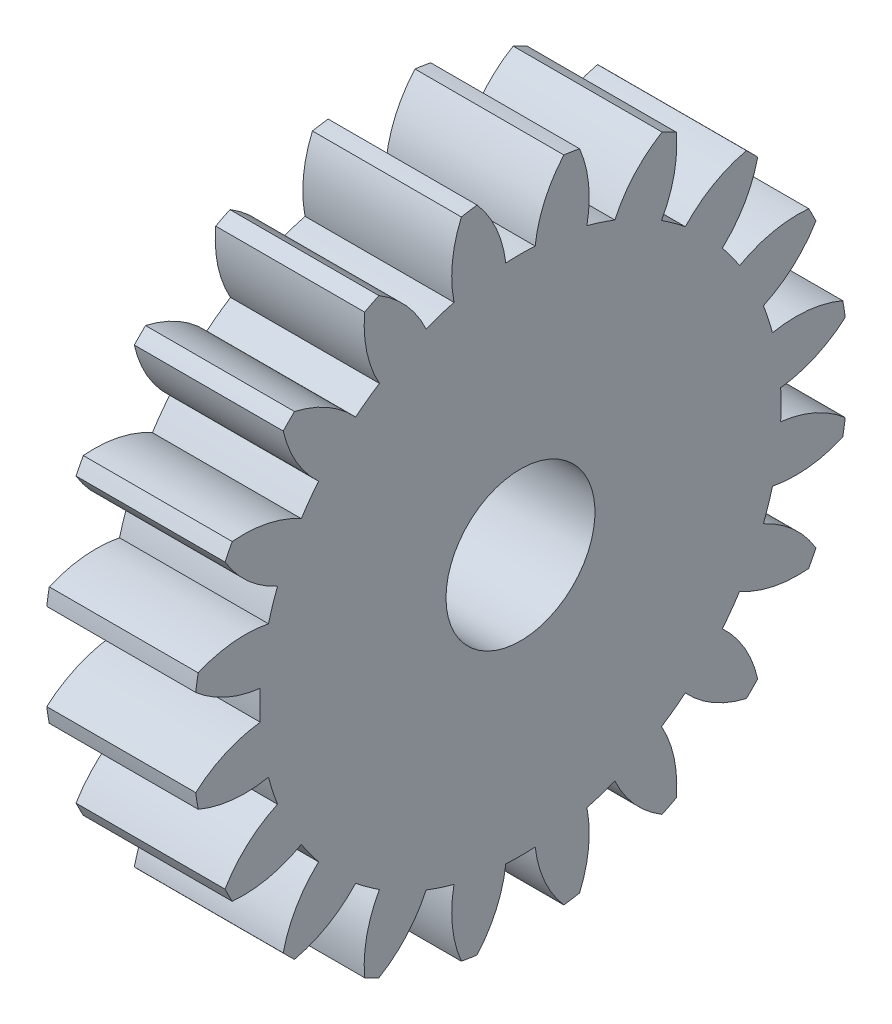
SolidWorks part; units mm, degrees
material "Pine"
ref_plane "Plane1" through (0, 0, 0) normal (0, 0, 1) x (1, 0, 0)
ref_plane "Plane2" through (0, 0, 0) normal (0, 1, 0) x (1, 0, 0)
ref_plane "Plane3" through (0, 0, 0) normal (1, 0, 0) x (0, 0, -1)
sketch "HoldingSke" plane through (0, 0, 0) normal (0, 1, 0) x (1, 0, 0)
  line L0 (0, 0) -> (0.4698, -0.171)
  line L1 (-15, 0) -> (100, 0) construction
  line L2 (0, 0) -> (-2.1039, 2.3779)
  line L3 (0, 0) -> (-11.863, 4.5341)
  line L4 (0, 0) -> (8.1152, 2.9537)
  line L5 (0, 0) -> (-46.8476, -17.4728)
  line L6 (0, 0) -> (-8.2896, -5.593)
  line L7 (-2.1039, 2.3779) -> (8.6586, 51.2059)
  line L8 (-76.2, 54.61) -> (-74.4, 54.61)
  line L9 (-71.009, 38.7566) -> (-53.1078, 45.2721)
  line L10 (-76.2, 71.12) -> (104.1128, 71.12)
  line L11 (0, 0) -> (-10, 0)
  line L12 (-76.2, 101.6) -> (-76.133, 101.6)
  line L13 (24.9733, 27.94) -> (52.9518, 28.4284)
  line L14 (24.9733, 27.94) -> (24.9743, 27.94)
  line L15 (24.9733, 27.94) -> (100.4006, 29.5858)
  line L16 (-63.627, -2) -> (-12.827, -2)
  circle A0 centre (0, 0) radius 5
  circle A1 centre (0, 0) radius 17.499
  circle A2 centre (0, 0) radius 37.5
  circle A3 centre (0, 0) radius 5
  dimension "MHD" = 34.998
  dimension "Hub_dia" = 75
  dimension "Bore" = 10
  dimension "MBD" = 10
  dimension "Num_teeth" = 20
  dimension "Pitch" = 0.5
  dimension "Overall_len" = 50
  dimension "Show_teeth" = 20
  dimension "Thickness" = 10
  dimension "OAL" = 50.0001
  dimension "T_dim" = 1.8
  dimension "Ap" = 20
  dimension "H" = 19.05
  dimension "Pitch_radius" = 180.3128
  dimension "Width" = 10
  dimension "Backlash" = 0.067
  dimension "Addendum_fac" = 1
  dimension "Dedendum_fac" = 1.25
  dimension "Clearance_fac" = 0.25
  dimension "Dedendum_add" = 0.001
  dimension "Module" = 2
sketch "BasProSke" plane through (0, 0, 0) normal (0, 1, 0) x (1, 0, 0)
  line L0 (-10, 0) -> (60, 0) construction
  line L1 (0, 0) -> (0, 22)
  line L2 (0, 0) -> (10, 0)
  line L3 (10, 0) -> (10, 22)
  line L4 (10, 22) -> (0, 22)
  dimension "Thickness" = 10
  dimension "Diameter" = 44
revolve "Base-Revolve" add sketch "BasProSke" angle 360 about L0
sketch "TooCutSke" plane through (0, 0, 0) normal (1, 0, 0) x (0, 0, -1)
  line L1 (0, 0) -> (0, 107) construction
  line L2 (0, 0) -> (-1.6864, 19.9288) construction
  line L3 (0, 0) -> (-6.2409, 39.4033) construction
  line L4 (-1.6864, 19.9288) -> (-3.1204, 19.7016) construction
  arc A0 (0.9862, 17.4712) -> (-0.9862, 17.4712) centre (0, 0) ccw
  arc A1 (2.9329, 21.8293) -> (-2.9329, 21.8293) centre (0, 0) ccw
  circle A2 centre (0, 0) radius 20 construction
  circle A3 centre (0, 0) radius 18.7939 construction
  arc A4 (-0.9862, 17.4712) -> (-2.9329, 21.8293) centre (-8.9313, 16.536) ccw
  arc A5 (2.9329, 21.8293) -> (0.9862, 17.4712) centre (8.9313, 16.536) ccw
  dimension "Root_dia" = 34.998
  dimension "Overcut_dia" = 44.0508
  dimension "Pitch_dia" = 40
  dimension "Base_dia" = 37.5877
  dimension "Flank_rad" = 8
  dimension "Half_ang" = 9
  dimension "Half_CT" = 1.4519
extrude "ToothCut" cut sketch "TooCutSke" along normal through all
fillet "Breaks" [suppressed] radius 0.04
fillet "RootFillets" [suppressed] radius 0.501
pattern_circular "TeethCuts" count 20 every 18 about axis through (-10, 0, 0) along (1, 0, 0) of "ToothCut", "RootFillets", "Breaks"
sketch "HubNeaOneSke" plane through (0, 0, 0) normal (-1, 0, 0) x (0, 0, 1)
  circle A0 centre (0, 0) radius 17.499
  dimension "Diameter" = 34.998
extrude "HubNearOne" [suppressed] add sketch "HubNeaOneSke" along normal blind 40.0001
sketch "HubNeaBotSke" plane through (0, 0, 0) normal (-1, 0, 0) x (0, 0, 1)
  circle A0 centre (0, 0) radius 17.499
  dimension "Diameter" = 34.998
extrude "HubNearBoth" [suppressed] add sketch "HubNeaBotSke" along normal blind 20
ref_plane "FarPln" through (10, 0, 0) normal (1, 0, 0) x (0, 0, -1)
sketch "HubFarSke" plane through (10, 0, 0) normal (1, 0, 0) x (0, 0, -1)
  circle A0 centre (0, 0) radius 17.499
  dimension "Diameter" = 34.998
extrude "HubFar" [suppressed] add sketch "HubFarSke" along normal blind 20
sketch "BorSke" plane through (0, 0, 0) normal (1, 0, 0) x (0, 0, -1)
  circle A0 centre (0, 0) radius 5
  dimension "Diameter" = 10
extrude "Bore" cut sketch "BorSke" along normal mid plane 100.0001
sketch "KeySke" plane through (0, 0, 0) normal (1, 0, 0) x (0, 0, -1)
  line L0 (-2, 0) -> (-2, 6.8)
  line L1 (-2, 6.8) -> (2, 6.8)
  line L2 (2, 6.8) -> (2, 0)
  line L3 (0, 0) -> (0, 34) construction
  line L4 (-2, 0) -> (2, 0)
  dimension "Offset" = 6.8
  dimension "Width" = 4
extrude "Keyway" [suppressed] cut sketch "KeySke" along normal mid plane 100.0001
pattern_circular "Keyway2" [suppressed] count 2 every 90 about axis through (-10, 0, 0) along (1, 0, 0)
equation "' \"Module@HoldingSke\" = 6.35"
equation "' \"Num_teeth@HoldingSke\" = 12"
equation "' \"Ap@HoldingSke\" =  20"
equation "' \"Ap@HoldingSke\" = 20"
equation "' \"Width@HoldingSke\" = 0.5 * 25.4"
equation "' \"Hub_dia@HoldingSke\"= 1 * 25.4"
equation "' \"Hub_dia@HoldingSke\" = 1 * 25.4"
equation "' \"Overall_len@HoldingSke\" = 1.0 * 25.4"
equation "' \"Bore@HoldingSke\" = 0.75 * 25.4"
equation "' \"T_dim@HoldingSke\" = 0.1 * 25.4"
equation "' \"Width@KeySke\" = 0.25 * 25.4"
equation "' \"Show_teeth@HoldingSke\" = 13"
equation "' \"Backlash@HoldingSke\" = 0.009 * 25.4"
equation "' \"Addendum_fac@HoldingSke\" = 1.0"
equation "' \"Dedendum_fac@HoldingSke\" = 1.25"
equation "' \"Dedendum_add@HoldingSke\" = 0.00005 * 25.4"
equation "' \"Clearance_fac@HoldingSke\" = 0.25"
equation "\"Pitch@HoldingSke\" = 1 / \"Module@HoldingSke\""
equation "\"Overcut_dia@TooCutSke\" = (\"Num_teeth@HoldingSke\" + 2 * \"Addendum_fac@HoldingSke\") / \"Pitch@HoldingSke\" + 0.002 * 25.4"
equation "\"Pitch_dia@TooCutSke\" = \"Num_teeth@HoldingSke\" / \"Pitch@HoldingSke\""
equation "\"Base_dia@TooCutSke\" = \"Num_teeth@HoldingSke\" / \"Pitch@HoldingSke\" * cos((\"Ap@HoldingSke\"  * 3.14159265 / 180))"
equation "\"Root_dia@TooCutSke\" = (\"Num_teeth@HoldingSke\" + 2) / \"Pitch@HoldingSke\" - 2 * (\"Addendum_fac@HoldingSke\" + \"Dedendum_fac@HoldingSke\") / \"Pitch@HoldingSke\" - \"Dedendum_add@HoldingSke\" * 2"
equation "\"Half_ang@TooCutSke\" = 180 / \"Num_teeth@HoldingSke\""
equation "\"Half_CT@TooCutSke\" = \"Num_teeth@HoldingSke\" / \"Pitch@HoldingSke\" * sin((3.14159265 / 2 / \"Num_teeth@HoldingSke\")) / 2 - 7 * \"Backlash@HoldingSke\" / 4"
equation "\"Flank_rad@TooCutSke\" = \"Num_teeth@HoldingSke\" / \"Pitch@HoldingSke\" / 5"
equation "\"Radius@RootFillets\" = \"Clearance_fac@HoldingSke\" / \"Pitch@HoldingSke\" + \"Dedendum_add@HoldingSke\""
equation "\"Break_rad@Breaks\" = 0.02 / \"Pitch@HoldingSke\""
equation "\"Thickness@HoldingSke\" = \"Width@HoldingSke\""
equation "\"OAL@HoldingSke\" = \"Thickness@HoldingSke\""
equation "\"MHD@HoldingSke\" = (\"Num_teeth@HoldingSke\" + 2) / \"Pitch@HoldingSke\" - 2 * (\"Addendum_fac@HoldingSke\" + \"Dedendum_fac@HoldingSke\")  / \"Pitch@HoldingSke\" - \"Dedendum_add@HoldingSke\" * 2"
equation "\"MBD@HoldingSke\" = (\"Num_teeth@HoldingSke\" + 2) / \"Pitch@HoldingSke\" - 2 * (\"Addendum_fac@HoldingSke\" + \"Dedendum_fac@HoldingSke\")  / \"Pitch@HoldingSke\" - \"Dedendum_add@HoldingSke\" * 2 - 0.002 * 25.4"
equation "\"MHD@HoldingSke\" = ((sgn( \"MHD@HoldingSke\" - \"Hub_dia@HoldingSke\" )-1)*( \"MHD@HoldingSke\" - \"Hub_dia@HoldingSke\" ))/-2+ \"Hub_dia@HoldingSke\""
equation "\"MBD@HoldingSke\" = ((sgn( \"MBD@HoldingSke\" - \"Bore@HoldingSke\" )-1)*( \"MBD@HoldingSke\" - \"Bore@HoldingSke\" ))/-2+ \"Bore@HoldingSke\""
equation "\"OAL@HoldingSke\" = ((sgn( \"OAL@HoldingSke\" - \"Overall_len@HoldingSke\" )+1)*( \"OAL@HoldingSke\" - \"Overall_len@HoldingSke\" ))/2 + \"Overall_len@HoldingSke\" + 0.000002 * 25.4"
equation "\"Num_teeth@TeethCuts\" = int( \"Show_teeth@HoldingSke\" ) + 1"
equation "\"Num_teeth@TeethCuts\" = ((sgn( \"Num_teeth@TeethCuts\" - \"Num_teeth@HoldingSke\" )-1)*( \"Num_teeth@TeethCuts\" - \"Num_teeth@HoldingSke\" ))/-2+ \"Num_teeth@HoldingSke\""
equation "\"Num_teeth@TeethCuts\" = ((sgn( \"Num_teeth@TeethCuts\" - 2.0)+1)*( \"Num_teeth@TeethCuts\" - 2.0))/2 +2.0"
equation "\"Angle@TeethCuts\" = 360.0 / \"Num_teeth@HoldingSke\""
equation "\"Diameter@BasProSke\" = (\"Num_teeth@HoldingSke\" + 2 * \"Addendum_fac@HoldingSke\") / \"Pitch@HoldingSke\""
equation "\"Thickness@BasProSke\"  = \"Thickness@HoldingSke\""
equation "' \"Fillet_rad@BasProSke\" =  \"Thickness@HoldingSke\" * 0.05"
equation "' \"Fillet_rad@BasProSke\" = \"Thickness@HoldingSke\" * 0.05"
equation "\"MHD@HoldingSke\" = ((sgn( \"MHD@HoldingSke\" - \"Root_dia@TooCutSke\" )-1)*( \"MHD@HoldingSke\" - \"Root_dia@TooCutSke\" ))/-2+ \"Root_dia@TooCutSke\""
equation "\"Diameter@HubNeaOneSke\" = \"MHD@HoldingSke\""
equation "\"Length@HubNearOne\" = \"OAL@HoldingSke\" - \"Thickness@BasProSke\""
equation "\"Diameter@HubNeaBotSke\" = \"MHD@HoldingSke\""
equation "\"Length@HubNearBoth\" = ( \"OAL@HoldingSke\" - \"Thickness@BasProSke\" ) / 2.0"
equation "\"Thickness@FarPln\" = \"Thickness@BasProSke\""
equation "\"Diameter@HubFarSke\" = \"MHD@HoldingSke\""
equation "\"Length@HubFar\" = ( \"OAL@HoldingSke\" - \"Thickness@BasProSke\" ) / 2.0"
equation "\"Diameter@BorSke\" = \"MBD@HoldingSke\""
equation "\"D1@Bore\" = \"OAL@HoldingSke\" * 2.0"
equation "\"D1@Keyway\" = \"OAL@HoldingSke\" * 2.0"
equation "\"Offset@KeySke\" = \"T_dim@HoldingSke\" + \"MBD@HoldingSke\" / 2.0"
